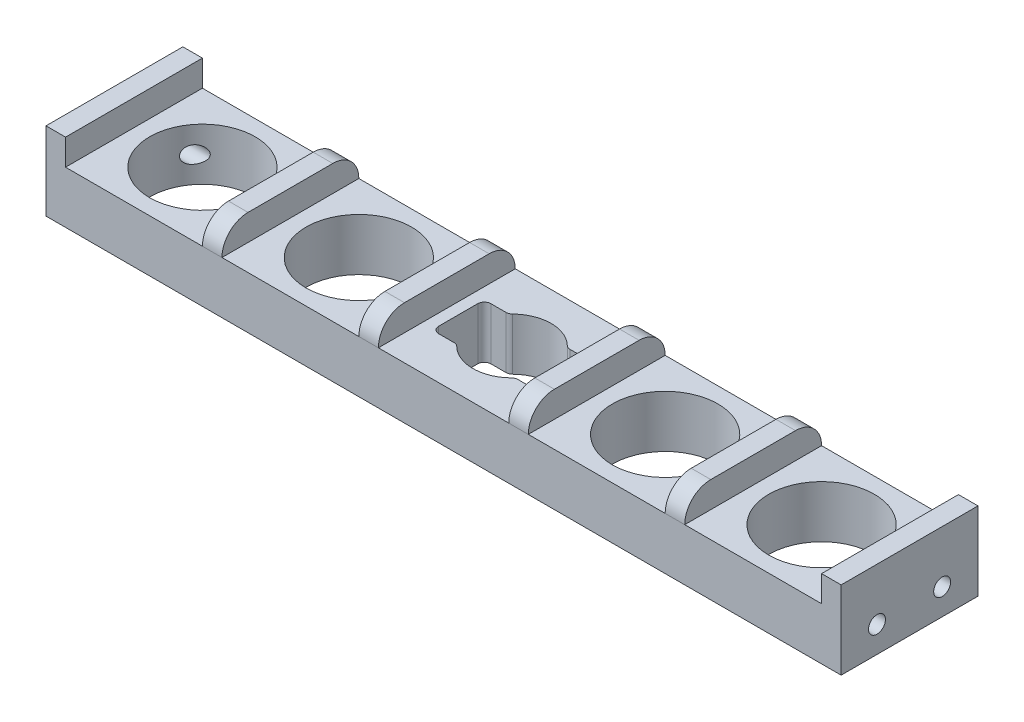
SolidWorks part; units mm, degrees
ref_plane "Front Plane" through (0, 0, 0) normal (0, 0, 1) x (1, 0, 0)
ref_plane "Top Plane" through (0, 0, 0) normal (0, 1, 0) x (1, 0, 0)
ref_plane "Right Plane" through (0, 0, 0) normal (1, 0, 0) x (0, 0, -1)
sketch "Sketch1" plane through (0, 0, 0) normal (0, 1, 0) x (1, 0, 0)
  line L1 (-61, 10.5) -> (61, 10.5)
  line L2 (-61, 10.5) -> (-61, -10.5)
  line L3 (-61, -10.5) -> (61, -10.5)
  line L4 (61, 10.5) -> (61, -10.5)
  line L5 (-61, 10.5) -> (61, -10.5) construction
  line L6 (-61, -10.5) -> (61, 10.5) construction
  circle A0 centre (23.5, 0) radius 10 construction
  circle A1 centre (47.5, 0) radius 10 construction
  circle A2 centre (-23.5, 0) radius 10 construction
  circle A3 centre (-47.5, 0) radius 10 construction
  circle A4 centre (-47.5, 0) radius 8.1
  circle A5 centre (-23.5, 0) radius 8.1
  circle A6 centre (23.5, 0) radius 8.1
  circle A7 centre (47.5, 0) radius 8.1
  point P0 (0, 0)
  dimension "D3" = 20
  dimension "D8" = 16.2
  dimension "D1" = 122
  dimension "D2" = 21
  dimension "D4" = 24
  dimension "D5" = 13.5
  dimension "D6" = 13.5
  dimension "D7" = 24
extrude "Boss-Extrude1" add sketch "Sketch1" along normal blind 8
sketch "Sketch4" plane through (0, 8, 0) normal (0, 1, 0) x (1, 0, 0)
  line L6 (-8.25, 4) -> (8.25, 4)
  line L7 (-8.25, 4) -> (-8.25, -4)
  line L8 (-8.25, -4) -> (8.25, -4)
  line L9 (8.25, 4) -> (8.25, -4)
  line L10 (-8.25, 4) -> (8.25, -4) construction
  line L11 (-8.25, -4) -> (8.25, 4) construction
  circle A0 centre (0, 0) radius 6
  point P0 (0, 0)
  dimension "D3" = 12
  dimension "D1" = 8
  dimension "D2" = 16.5
extrude "Cut-Extrude1" cut sketch "Sketch4" against normal blind 122 contours A0 L8 L9 L6 | L8 A0 L6 | L6 A0 | L8 A0 | A0 L6 L7 L8
fillet "Fillet2" radius 1 8 edges at (-8.25, 4, 4) (-4.4721, 4, 4) (4.4721, 4, 4) (8.25, 4, 4) (8.25, 4, -4) (4.4721, 4, -4) (-4.4721, 4, -4) (-8.25, 4, -4)
sketch "Sketch6" plane through (0, 8, 0) normal (0, 1, 0) x (1, 0, 0)
  line L0 (-61, -10.5) -> (61, -10.5) construction
  line L1 (-61, 10.5) -> (-58, 10.5)
  line L2 (-61, 10.5) -> (-61, -10.5)
  line L3 (-61, -10.5) -> (-58, -10.5)
  line L4 (-58, 10.5) -> (-58, -10.5)
  line L5 (61, 10.5) -> (-61, 10.5) construction
  line L6 (-37, 10.5) -> (-34, 10.5)
  line L7 (-37, 10.5) -> (-37, -10.5)
  line L8 (-37, -10.5) -> (-34, -10.5)
  line L9 (-34, 10.5) -> (-34, -10.5)
  line L10 (-35.5, 10.5) -> (-35.5, -10.5) construction
  line L19 (34, 10.5) -> (37, 10.5)
  line L20 (34, 10.5) -> (34, -10.5)
  line L21 (34, -10.5) -> (37, -10.5)
  line L22 (37, 10.5) -> (37, -10.5)
  line L23 (61, 10.5) -> (58, 10.5)
  line L24 (61, 10.5) -> (61, -10.5)
  line L25 (61, -10.5) -> (58, -10.5)
  line L26 (58, 10.5) -> (58, -10.5)
  line L27 (-59.5, 10.5) -> (-59.5, -10.5) construction
  line L28 (-11.5, 10.5) -> (-11.5, -10.5) construction
  line L29 (35.5, -10.5) -> (35.5, 10.5) construction
  line L30 (-13, 10.5) -> (-10, 10.5)
  line L31 (-13, 10.5) -> (-13, -10.5)
  line L32 (-13, -10.5) -> (-10, -10.5)
  line L33 (-10, 10.5) -> (-10, -10.5)
  line L34 (10, 10.5) -> (13, 10.5)
  line L35 (10, 10.5) -> (10, -10.5)
  line L36 (10, -10.5) -> (13, -10.5)
  line L37 (13, 10.5) -> (13, -10.5)
  line L38 (11.5, -10.5) -> (11.5, 10.5) construction
  circle A0 centre (-47.5, 0) radius 8.1 construction
  circle A2 centre (47.5, 0) radius 8.1 construction
  circle A3 centre (-23.5, 0) radius 8.1 construction
  circle A4 centre (23.5, 0) radius 8.1 construction
  dimension "D4" = 12
  dimension "D1" = 3
  dimension "D2" = 3
  dimension "D3" = 12
  dimension "D5" = 3
  dimension "D6" = 3
  dimension "D7" = 12
  dimension "D8" = 12
  dimension "D9" = 3
  dimension "D10" = 3
extrude "Boss-Extrude4" add sketch "Sketch6" along normal blind 4
fillet "Fillet3" radius 4 8 edges at (35.5, 12, 10.5) (11.5, 12, 10.5) (-11.5, 12, 10.5) (-35.5, 12, 10.5) (35.5, 12, -10.5) (11.5, 12, -10.5) (-11.5, 12, -10.5) (-35.5, 12, -10.5)
sketch "Sketch7" plane through (61, 0, 0) normal (1, 0, 0) x (0, 0, -1)
  line L0 (-10.5, 0) -> (10.5, 0) construction
  circle A0 centre (-5, 4) radius 1.3
  circle A1 centre (5, 4) radius 1.3
  dimension "D4" = 2.6
  dimension "D1" = 4
  dimension "D2" = 5
  dimension "D3" = 5
extrude "Cut-Extrude2" cut sketch "Sketch7" against normal blind 10
mirror "Mirror1" about plane through (0, 0, 0) normal (1, 0, 0) of "Cut-Extrude2"
